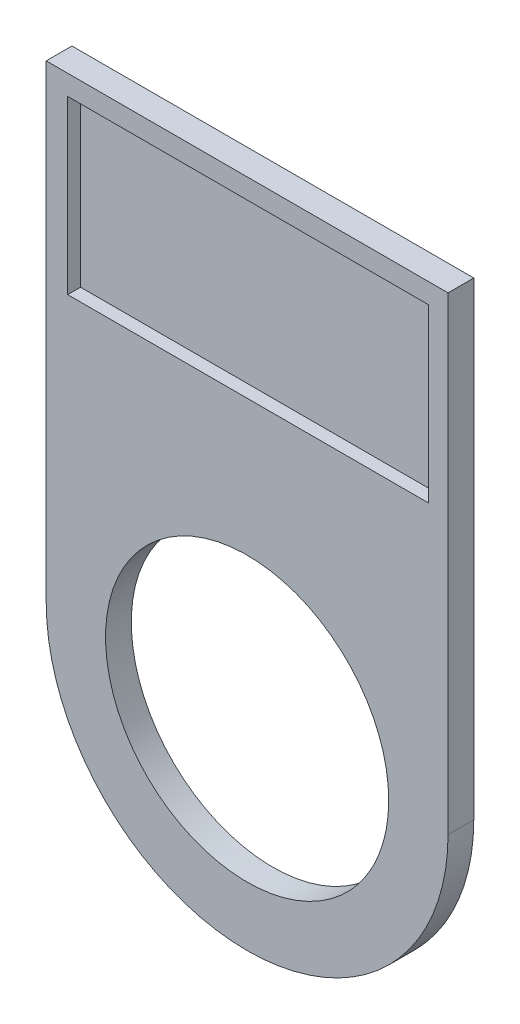
SolidWorks part; units mm, degrees
ref_plane "Front Plane" through (0, 0, 0) normal (0, 0, 1) x (1, 0, 0)
ref_plane "Top Plane" through (0, 0, 0) normal (0, 1, 0) x (1, 0, 0)
ref_plane "Right Plane" through (0, 0, 0) normal (1, 0, 0) x (0, 0, -1)
sketch "Sketch1" plane through (0, 0, 0) normal (0, 0, 1) x (1, 0, 0)
  line L0 (420.8083, 971.7945) -> (420.8083, 1008.2446)
  line L1 (420.8083, 1008.2446) -> (452.0243, 1008.2446)
  line L2 (452.0243, 1008.2446) -> (452.0243, 971.7945)
  line L3 (422.4765, 1006.6889) -> (450.5019, 1006.6889)
  line L4 (450.5019, 1006.6889) -> (450.5019, 993.3506)
  line L5 (450.5019, 993.3506) -> (422.4765, 993.3506)
  line L6 (422.4765, 993.3506) -> (422.4765, 1006.6889)
  line L8 (422.4765, 1006.6889) -> (450.5019, 1006.6889)
  line L9 (422.4765, 1006.6889) -> (422.4765, 993.3506)
  line L10 (422.4765, 993.3506) -> (450.5019, 993.3506)
  line L11 (450.5019, 1006.6889) -> (450.5019, 993.3506)
  circle A0 centre (436.4163, 971.7945) radius 11
  arc A1 (420.8083, 971.7945) -> (452.0243, 971.7945) centre (436.4163, 971.7945) ccw
sketch "Sketch2" plane through (0, 0, 0) normal (0, 0, 1) x (1, 0, 0)
  line L1 (422.4765, 1006.6889) -> (450.5019, 1006.6889)
  line L2 (422.4765, 1006.6889) -> (422.4765, 993.3506)
  line L3 (422.4765, 993.3506) -> (450.5019, 993.3506)
  line L4 (450.5019, 1006.6889) -> (450.5019, 993.3506)
extrude "Boss-Extrude1" add sketch "Sketch1" along normal blind 2 contours L0 A1 L2 L1 L5 L6 L3 L4 A0
extrude "Boss-Extrude2" add sketch "Sketch2" along normal blind 1
